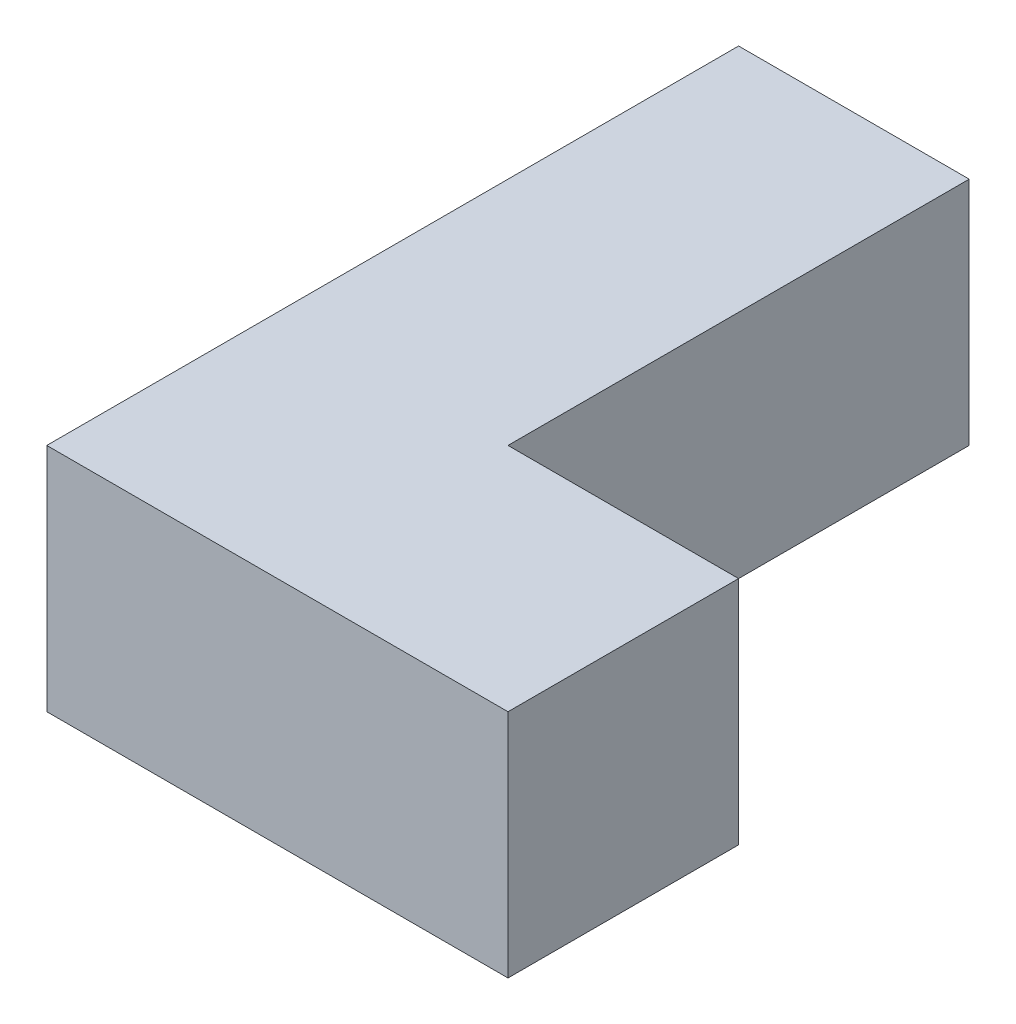
SolidWorks part; units mm, degrees
ref_plane "Front Plane" through (0, 0, 0) normal (0, 0, 1) x (1, 0, 0)
ref_plane "Top Plane" through (0, 0, 0) normal (0, 1, 0) x (1, 0, 0)
ref_plane "Right Plane" through (0, 0, 0) normal (1, 0, 0) x (0, 0, -1)
sketch "Sketch1" plane through (0, 0, 0) normal (0, 1, 0) x (1, 0, 0)
  line L0 (-5000, 7500) -> (-5000, -7500)
  line L1 (-5000, -7500) -> (5000, -7500)
  line L2 (5000, -7500) -> (5000, -2500)
  line L3 (5000, -2500) -> (0, -2500)
  line L4 (0, -2500) -> (0, 7500)
  line L5 (0, 7500) -> (-5000, 7500)
  dimension "D1" = 5000
  dimension "D2" = 10000
  dimension "D3" = 5000
  dimension "D4" = 5000
  dimension "D5" = 2500
  dimension "D6" = 0
extrude "Boss-Extrude1" add sketch "Sketch1" along normal blind 5000
